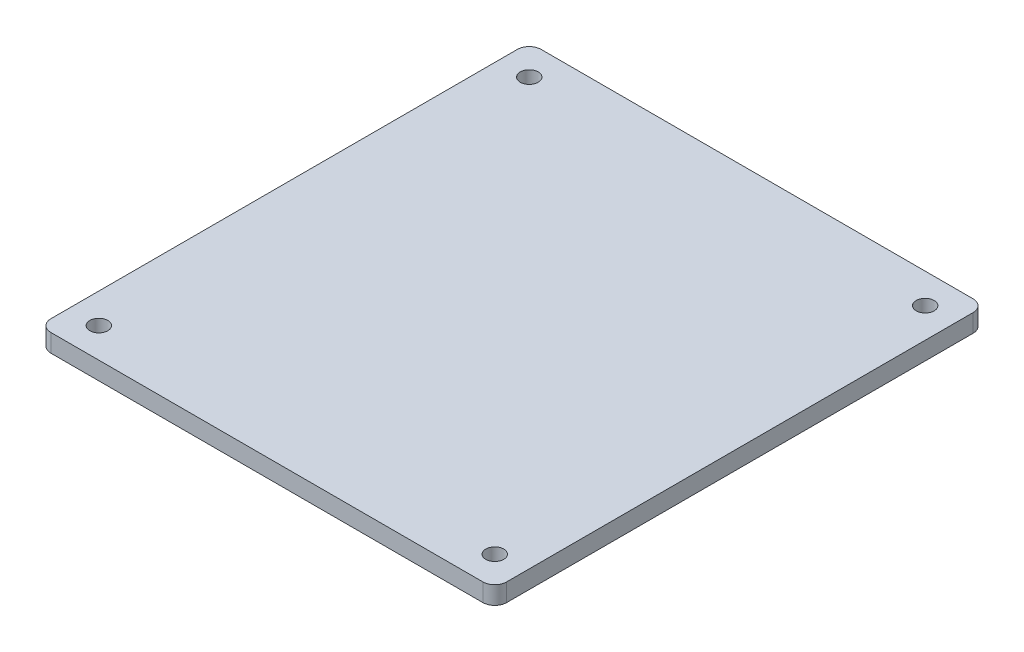
SolidWorks part; units mm, degrees
ref_plane "Front Plane" through (0, 0, 0) normal (0, 0, 1) x (1, 0, 0)
ref_plane "Top Plane" through (0, 0, 0) normal (0, 1, 0) x (1, 0, 0)
ref_plane "Right Plane" through (0, 0, 0) normal (1, 0, 0) x (0, 0, -1)
sketch "Sketch1" plane through (0, 0, 0) normal (0, 1, 0) x (1, 0, 0)
  line L1 (1.5875, 0) -> (58.8645, 0)
  line L2 (0, 1.5875) -> (0, 63.4365)
  line L3 (1.5875, 65.024) -> (58.8645, 65.024)
  line L4 (60.452, 1.5875) -> (60.452, 63.4365)
  circle A0 centre (3.9688, 3.9688) radius 1.1906
  circle A1 centre (3.9688, 61.0553) radius 1.1906
  circle A2 centre (56.4832, 61.0553) radius 1.1906
  circle A3 centre (56.4832, 3.9688) radius 1.1906
  arc A4 (1.5875, 0) -> (0, 1.5875) centre (1.5875, 1.5875) cw
  arc A5 (60.452, 1.5875) -> (58.8645, 0) centre (58.8645, 1.5875) cw
  arc A6 (60.452, 63.4365) -> (58.8645, 65.024) centre (58.8645, 63.4365) ccw
  arc A7 (1.5875, 65.024) -> (0, 63.4365) centre (1.5875, 63.4365) ccw
  point P15 (0, 0)
  dimension "D1" = 1.5875
extrude "Boss-Extrude1" add sketch "Sketch1" along normal blind 2.3813
